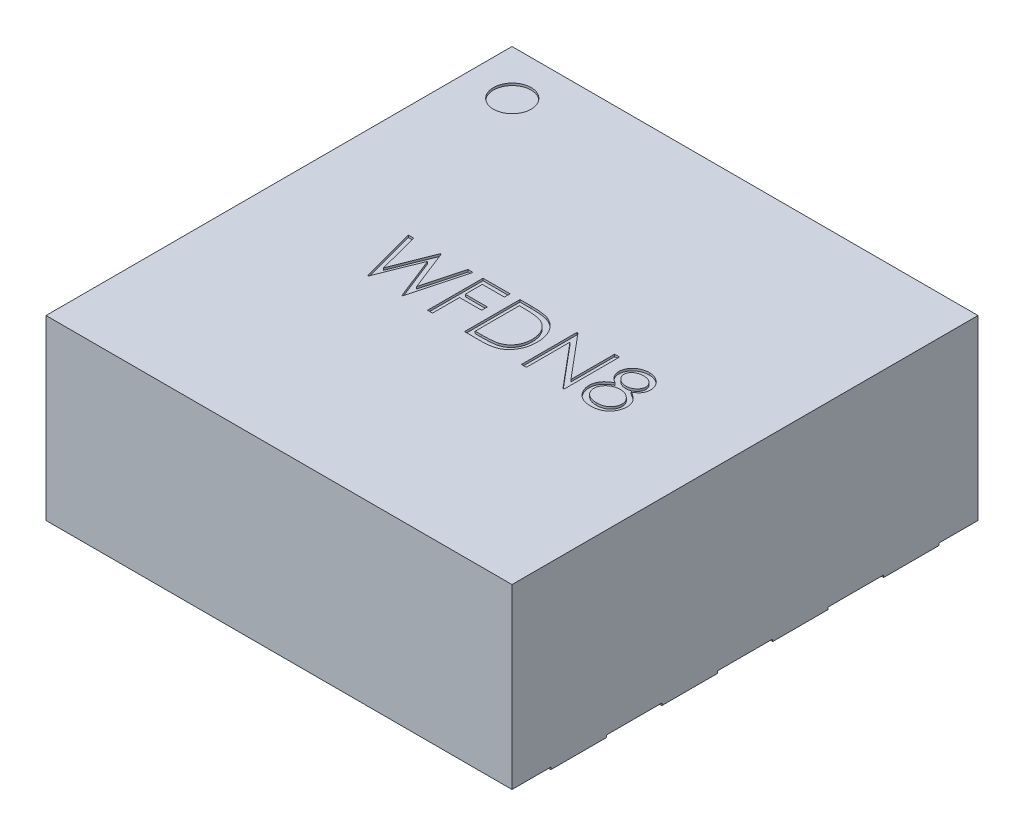
SolidWorks part; units mm, degrees
ref_plane "Front Plane" through (0, 0, 0) normal (0, 0, 1) x (1, 0, 0)
ref_plane "Top Plane" through (0, 0, 0) normal (0, 1, 0) x (1, 0, 0)
ref_plane "Right Plane" through (0, 0, 0) normal (1, 0, 0) x (0, 0, -1)
sketch "Sketch1" plane through (0, 0, 0) normal (0, 1, 0) x (1, 0, 0)
  line L1 (-1.05, 1.05) -> (1.05, 1.05)
  line L2 (-1.05, 1.05) -> (-1.05, -1.05)
  line L3 (-1.05, -1.05) -> (1.05, -1.05)
  line L4 (1.05, 1.05) -> (1.05, -1.05)
  line L5 (-1.05, 1.05) -> (1.05, -1.05) construction
  line L6 (-1.05, -1.05) -> (1.05, 1.05) construction
  point P0 (0, 0)
  dimension "D1" = 2.1
  dimension "D2" = 2.1
extrude "Boss-Extrude1" add sketch "Sketch1" along normal blind 0.8
sketch "Sketch2" plane through (0, 0, 0) normal (0, -1, 0) x (1, 0, 0)
  line L0 (-1.05, -1.05) -> (-1.05, 1.05) construction
  line L1 (-1.05, -0.625) -> (-0.75, -0.625)
  line L2 (-1.05, -0.625) -> (-1.05, -0.875)
  line L3 (-1.05, -0.875) -> (-0.75, -0.875)
  line L4 (-0.75, -0.625) -> (-0.75, -0.875)
  line L5 (-0.75, -0.75) -> (-1.05, -0.75) construction
  line L6 (-1.05, -0.125) -> (-0.75, -0.125)
  line L7 (-1.05, -0.125) -> (-1.05, -0.375)
  line L8 (-1.05, -0.375) -> (-0.75, -0.375)
  line L9 (-0.75, -0.125) -> (-0.75, -0.375)
  line L10 (-0.75, -0.25) -> (-1.05, -0.25) construction
  line L11 (-1.05, 0.375) -> (-0.75, 0.375)
  line L12 (-1.05, 0.375) -> (-1.05, 0.125)
  line L13 (-1.05, 0.125) -> (-0.75, 0.125)
  line L14 (-0.75, 0.375) -> (-0.75, 0.125)
  line L15 (-0.75, 0.25) -> (-1.05, 0.25) construction
  line L16 (-1.05, 0.875) -> (-0.75, 0.875)
  line L17 (-1.05, 0.875) -> (-1.05, 0.625)
  line L18 (-1.05, 0.625) -> (-0.75, 0.625)
  line L19 (-0.75, 0.875) -> (-0.75, 0.625)
  line L20 (-0.75, 0.75) -> (-1.05, 0.75) construction
  line L21 (-0.75, 0.875) -> (-1.05, 1.05) construction
  line L22 (-0.75, -0.875) -> (-1.05, -1.05) construction
  line L23 (0, 1.05) -> (0, -1.05) construction
  line L24 (-1.05, 1.05) -> (1.05, 1.05) construction
  line L25 (1.05, -1.05) -> (-1.05, -1.05) construction
  line L26 (0.75, -0.875) -> (1.05, -1.05) construction
  line L27 (0.75, 0.875) -> (1.05, 1.05) construction
  line L28 (0.75, 0.75) -> (1.05, 0.75) construction
  line L29 (0.75, 0.25) -> (1.05, 0.25) construction
  line L30 (0.75, -0.25) -> (1.05, -0.25) construction
  line L31 (0.75, -0.75) -> (1.05, -0.75) construction
  line L32 (0.75, 0.875) -> (0.75, 0.625)
  line L33 (1.05, 0.625) -> (0.75, 0.625)
  line L34 (1.05, 0.875) -> (1.05, 0.625)
  line L35 (1.05, 0.875) -> (0.75, 0.875)
  line L36 (0.75, 0.375) -> (0.75, 0.125)
  line L37 (1.05, 0.125) -> (0.75, 0.125)
  line L38 (1.05, 0.375) -> (1.05, 0.125)
  line L39 (1.05, 0.375) -> (0.75, 0.375)
  line L40 (0.75, -0.125) -> (0.75, -0.375)
  line L41 (1.05, -0.375) -> (0.75, -0.375)
  line L42 (1.05, -0.125) -> (1.05, -0.375)
  line L43 (1.05, -0.125) -> (0.75, -0.125)
  line L44 (0.75, -0.625) -> (0.75, -0.875)
  line L45 (1.05, -0.875) -> (0.75, -0.875)
  line L46 (1.05, -0.625) -> (1.05, -0.875)
  line L47 (1.05, -0.625) -> (0.75, -0.625)
  line L48 (-0.45, 0.8) -> (-0.45, -0.5733)
  line L49 (-0.45, 0.8) -> (0.45, 0.8)
  line L50 (-0.45, -0.5733) -> (-0.0956, -0.8)
  line L51 (-0.0956, -0.8) -> (0.45, -0.8)
  line L52 (0.45, 0.8) -> (0.45, -0.8)
  line L53 (0, 0) -> (1.05, 0) construction
  line L54 (1.05, 1.05) -> (1.05, -1.05) construction
  point P64 (0, 0.8)
  point P73 (0.45, 0)
  dimension "D1" = 0.25
  dimension "D2" = 0.3
  dimension "D4" = 0.5
  dimension "D5" = 0.9
  dimension "D6" = 1.6
  dimension "D3" = 4
extrude "Boss-Extrude2" add sketch "Sketch2" along normal blind 0.01
sketch "Sketch3" plane through (0, 0.8, 0) normal (0, 1, 0) x (1, 0, 0)
  circle A0 centre (-0.8468, 0.8481) radius 0.0848
  text T0 "WFDN8" font "Century Gothic" height 0.25
extrude "Cut-Extrude1" cut sketch "Sketch3" against normal blind 0.01
